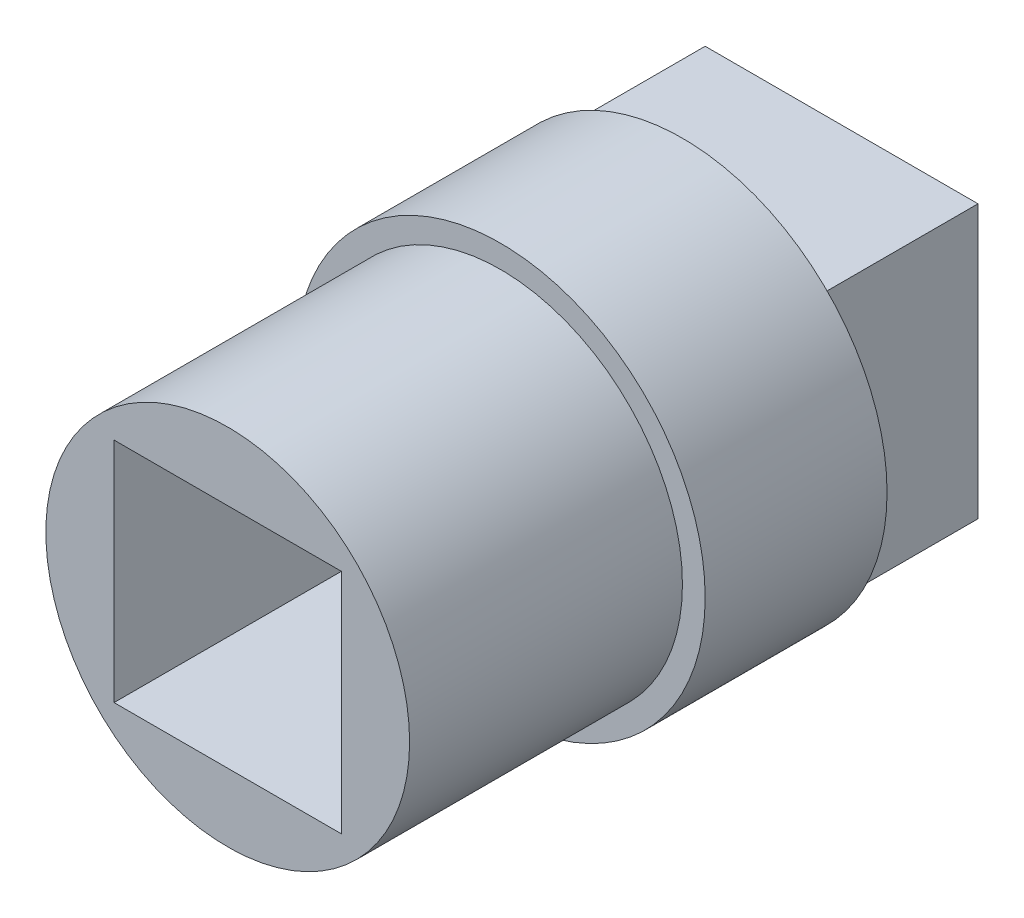
SolidWorks part; units mm, degrees
ref_plane "Alzado" through (0, 0, 0) normal (0, 0, 1) x (1, 0, 0)
ref_plane "Planta" through (0, 0, 0) normal (0, 1, 0) x (1, 0, 0)
ref_plane "Vista lateral" through (0, 0, 0) normal (1, 0, 0) x (0, 0, -1)
sketch "Croquis1" plane through (0, 0, 0) normal (0, 0, 1) x (1, 0, 0)
  line L1 (-3, -3) -> (3, -3)
  line L2 (-3, -3) -> (-3, 3)
  line L3 (-3, 3) -> (3, 3)
  line L4 (3, -3) -> (3, 3)
  line L5 (-3, -3) -> (3, 3) construction
  line L6 (-3, 3) -> (3, -3) construction
  point P0 (0, 0)
  dimension "D1" = 6
  dimension "D2" = 6
extrude "Saliente-Extruir1" add sketch "Croquis1" along normal blind 3.5
sketch "Croquis2" plane through (0, 0, 3.5) normal (0, 0, 1) x (1, 0, 0)
  circle A0 centre (0, 0) radius 4.5
  dimension "D1" = 9
extrude "Saliente-Extruir2" add sketch "Croquis2" along normal blind 4
sketch "Croquis3" plane through (0, 0, 7.5) normal (0, 0, 1) x (1, 0, 0)
  circle A0 centre (0, 0) radius 4
  dimension "D1" = 8
extrude "Saliente-Extruir3" add sketch "Croquis3" along normal blind 6
ref_plane "Plano1" through (0, 0, 0) normal (1, 0, 0) x (0, 0, -1)
sketch "Croquis4" plane through (0, 0, 13.5) normal (0, 0, 1) x (1, 0, 0)
  line L1 (-2.5, -2.5) -> (2.5, -2.5)
  line L2 (-2.5, -2.5) -> (-2.5, 2.5)
  line L3 (-2.5, 2.5) -> (2.5, 2.5)
  line L4 (2.5, -2.5) -> (2.5, 2.5)
  line L5 (-2.5, -2.5) -> (2.5, 2.5) construction
  line L6 (-2.5, 2.5) -> (2.5, -2.5) construction
  point P0 (0, 0)
  dimension "D1" = 5
  dimension "D2" = 5
extrude "Cortar-Extruir1" cut sketch "Croquis4" against normal blind 5
